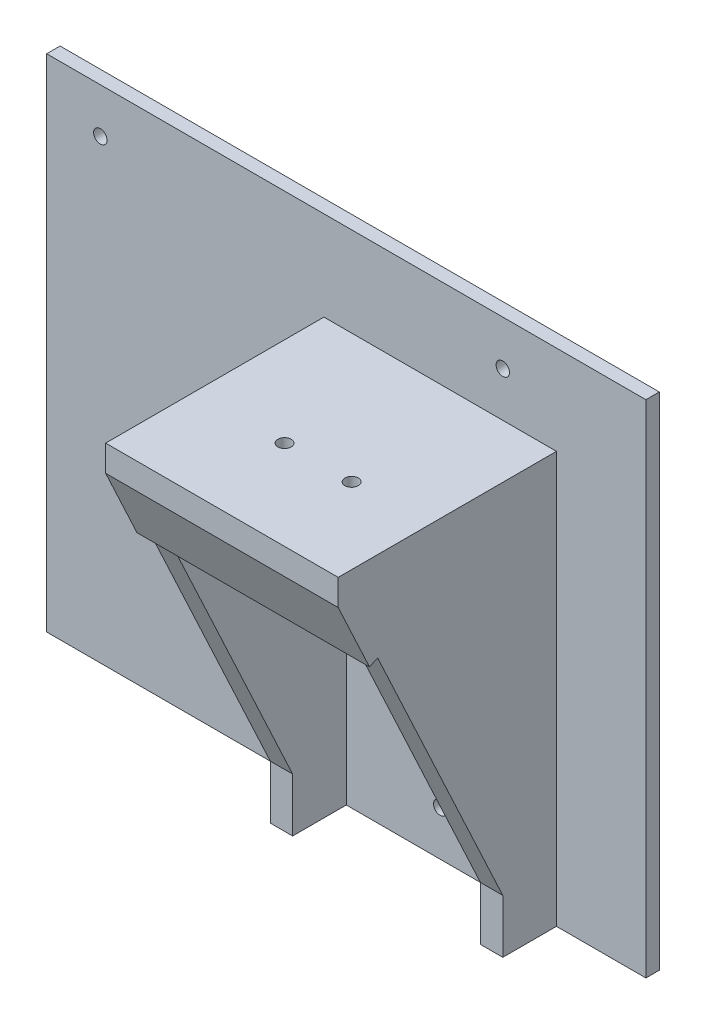
SolidWorks part; units mm, degrees
ref_plane "Front" through (0, 0, 0) normal (0, 0, 1) x (1, 0, 0)
ref_plane "Top" through (0, 0, 0) normal (0, 1, 0) x (1, 0, 0)
ref_plane "Right" through (0, 0, 0) normal (1, 0, 0) x (0, 0, -1)
sketch "Sketch1" plane through (0, 0, 0) normal (0, 0, 1) x (1, 0, 0)
  line L1 (-36, -46) -> (36, -46)
  line L2 (-36, -46) -> (-36, 46)
  line L3 (-36, 46) -> (36, 46)
  line L4 (36, -46) -> (36, 46)
  line L5 (-36, -46) -> (36, 46) construction
  line L6 (-36, 46) -> (36, -46) construction
  point P0 (0, 0)
  dimension "D1" = 92
  dimension "D2" = 72
extrude "Boss-Extrude1" add sketch "Sketch1" along normal blind 3
sketch "Sketch2" plane through (0, 0, 3) normal (0, 0, 1) x (1, 0, 0)
  line L0 (36, 46) -> (-36, 46) construction
  line L1 (36, -46) -> (31, -46)
  line L2 (36, -46) -> (36, 46)
  line L3 (36, 46) -> (31, 46)
  line L4 (31, -46) -> (31, 46)
  line L5 (36, -46) -> (31, 46) construction
  line L6 (36, 46) -> (31, -46) construction
  line L7 (-36, -46) -> (36, -46) construction
  line L8 (-11, -46) -> (-16, -46)
  line L9 (-11, -46) -> (-11, 46)
  line L10 (-11, 46) -> (-16, 46)
  line L11 (-16, -46) -> (-16, 46)
  line L12 (-11, -46) -> (-16, 46) construction
  line L13 (-11, 46) -> (-16, -46) construction
  point P4 (33.5, 0)
  point P12 (-13.5, 0)
  dimension "D1" = 5
  dimension "D2" = 5
  dimension "D3" = 42
extrude "Boss-Extrude2" add sketch "Sketch2" along normal blind 47
sketch "Sketch3" plane through (0, 0, 50) normal (0, 0, 1) x (1, 0, 0)
  line L0 (36, -46) -> (36, 46) construction
  line L1 (-16, 46) -> (36, 46)
  line L2 (-16, 46) -> (-16, 26)
  line L3 (-16, 26) -> (36, 26)
  line L4 (36, 46) -> (36, 26)
  line L5 (-16, 46) -> (36, 26) construction
  line L6 (-16, 26) -> (36, 46) construction
  point P4 (10, 36)
  dimension "D1" = 20
extrude "Boss-Extrude3" add sketch "Sketch3" against normal up to next
sketch "Sketch7" plane through (-16, 0, 0) normal (-1, 0, 0) x (0, 0, 1)
  line L0 (50, 41) -> (15, -34)
  line L1 (50, 46) -> (50, -46) construction
  line L5 (50, 46) -> (3, 46) construction
  line L6 (50, 41) -> (50, -46)
  line L8 (50, -46) -> (50, 26) construction
  line L9 (50, -46) -> (50, 26)
  line L10 (15, -34) -> (15, -46)
  line L11 (50, -46) -> (3, -46) construction
  line L12 (15, -46) -> (50, -46)
  line L14 (3, 46) -> (3, -46) construction
  line M3 (3, -46) -> (50, -46)
  line M4 (50, -46) -> (50, 46)
  dimension "D1" = 12
  dimension "D2" = 5
  dimension "D3" = 12
extrude "Cut-Extrude3" cut sketch "Sketch7" against normal up to next contours L6 L0 M4 M3
sketch "Sketch8" plane through (0, -11.8285, 25.3467) normal (0, -0.4229, 0.9062) x (1, 0, 0)
  line L0 (36, -24.4669) -> (36, 58.2978) construction
  line L1 (-16, 58.2978) -> (36, 58.2978)
  line L2 (-16, 58.2978) -> (-16, 41.7448)
  line L3 (-16, 41.7448) -> (36, 41.7448)
  line L4 (36, 58.2978) -> (36, 41.7448)
  line L5 (-16, 58.2978) -> (36, 41.7448) construction
  line L6 (-16, 41.7448) -> (36, 58.2978) construction
  line L7 (31, 41.7448) -> (-11, 41.7448) construction
  point P4 (10, 50.0213)
extrude "Boss-Extrude5" add sketch "Sketch8" along normal blind 2
sketch "Sketch9" plane through (0, 0, 50) normal (0, 0, 1) x (1, 0, 0)
  line L0 (36, 40.1542) -> (-16, 40.1542) construction
  line L1 (36, 40.1542) -> (-16, 40.1542)
  line L3 (-16, 40.1542) -> (36, 40.1542)
  line L4 (-16, 40.1542) -> (-16, 46)
  line L5 (-16, 46) -> (36, 46)
  line L6 (36, 40.1542) -> (36, 46)
  line L7 (-16, 40.1542) -> (36, 46) construction
  line L8 (-16, 46) -> (36, 40.1542) construction
  point P5 (10, 43.0771)
  line M1 (-16, 41) -> (36, 41)
  line M2 (36, 41) -> (36, 46)
  line M3 (36, 46) -> (-16, 46)
  line M4 (-16, 46) -> (-16, 41)
extrude "Boss-Extrude6" add sketch "Sketch9" along normal up to vertex (1.8124 mm away) contours M4 M1 M2 M3 | L1 L6 L4 M1
sketch "Sketch10" plane through (0, 26, 0) normal (0, -1, 0) x (1, 0, 0)
  line L4 (31, 43) -> (-11, 43)
  line L5 (-11, 43) -> (-11, 3)
  line L6 (-11, 3) -> (31, 3)
  line L7 (31, 3) -> (31, 43)
  line L8 (31, 43) -> (-11, 43)
  line L9 (-11, 43) -> (-11, 3)
  line L10 (-11, 3) -> (31, 3)
  line L11 (31, 3) -> (31, 43)
  dimension "D1" = 0
extrude "Cut-Extrude4" cut sketch "Sketch10" against normal blind 17
sketch "Sketch12" plane through (0, 46, 0) normal (0, 1, 0) x (1, 0, 0)
  line L0 (-16, -31.8124) -> (36, -31.8124) construction
  line L1 (-16, -51.8124) -> (-16, -3) construction
  line L2 (36, -51.8124) -> (36, 0) construction
  line L3 (36, -51.8124) -> (-16, -51.8124) construction
  circle A0 centre (4, -31.8124) radius 1.5
  circle A1 centre (19, -31.8124) radius 1.5
  dimension "D2" = 3
  dimension "D3" = 3
  dimension "D4" = 20
  dimension "D5" = 15
  dimension "D1" = 20
extrude "Cut-Extrude5" cut sketch "Sketch12" against normal up to next
sketch "Sketch13" plane through (0, 46, 0) normal (0, 1, 0) x (1, 0, 0)
  line L1 (36, 0) -> (-36, 0)
  line L2 (36, 0) -> (36, -3)
  line L3 (36, -3) -> (-36, -3)
  line L4 (-36, 0) -> (-36, -3)
  line L5 (36, 0) -> (-36, -3) construction
  line L6 (36, -3) -> (-36, 0) construction
  point P4 (0, -1.5)
extrude "Boss-Extrude7" add sketch "Sketch13" along normal blind 20
sketch "Sketch15" plane through (36, 0, 0) normal (1, 0, 0) x (0, 0, -1)
  line L1 (0, -46) -> (-3, -46)
  line L2 (0, -46) -> (0, 66)
  line L3 (0, 66) -> (-3, 66)
  line L4 (-3, -46) -> (-3, 66)
  line L5 (0, -46) -> (-3, 66) construction
  line L6 (0, 66) -> (-3, -46) construction
  point P4 (-1.5, 10)
extrude "Boss-Extrude8" add sketch "Sketch15" along normal blind 20
sketch "Sketch16" plane through (-36, 0, 0) normal (-1, 0, 0) x (0, 0, 1)
  line L4 (0, 66) -> (0, -46)
  line L5 (0, -46) -> (3, -46)
  line L6 (3, -46) -> (3, 66)
  line L7 (3, 66) -> (0, 66)
  line L8 (0, 66) -> (0, -46)
  line L9 (0, -46) -> (3, -46)
  line L10 (3, -46) -> (3, 66)
  line L11 (3, 66) -> (0, 66)
  dimension "D1" = 0
extrude "Boss-Extrude9" add sketch "Sketch16" along normal blind 42
sketch "Sketch14" plane through (0, 0, 3) normal (0, 0, 1) x (1, 0, 0)
  line L0 (-78, 66) -> (56, 66) construction
  line L1 (-78, -46) -> (-78, 66) construction
  line L2 (-11, -46) -> (31, -46) construction
  line L5 (56, 66) -> (56, -46) construction
  line L9 (-11, -46) -> (-11, 43) construction
  circle A0 centre (24, 56) radius 1.5
  circle A1 centre (10, -36) radius 1.5
  circle A2 centre (-66, 56) radius 1.5
  dimension "D1" = 3
  dimension "D4" = 3
  dimension "D6" = 3
  dimension "D7" = 21
  dimension "D8" = 12
  dimension "D2" = 10
  dimension "D3" = 32
  dimension "D5" = 10
extrude "Cut-Extrude9" cut sketch "Sketch14" against normal up to next
